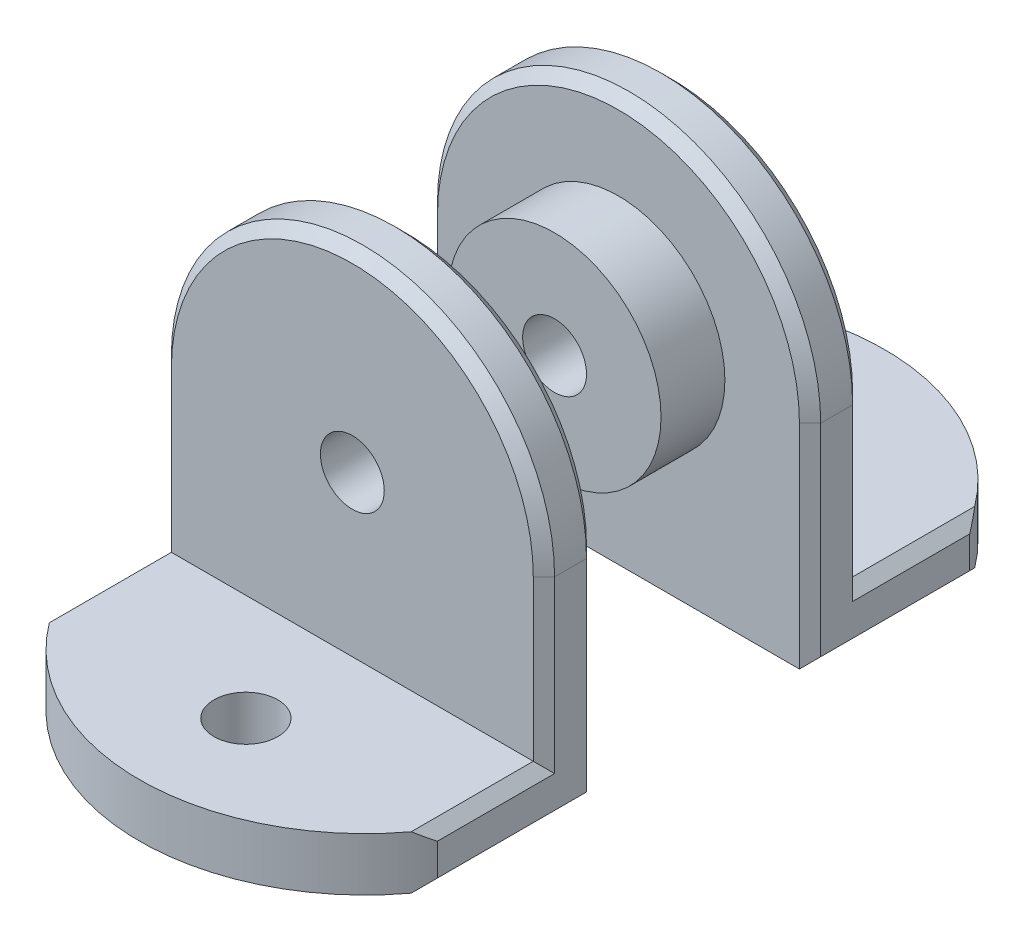
SolidWorks part; units mm, degrees
ref_plane "Front Plane" through (0, 0, 0) normal (0, 0, 1) x (1, 0, 0)
ref_plane "Top Plane" through (0, 0, 0) normal (0, 1, 0) x (1, 0, 0)
ref_plane "Right Plane" through (0, 0, 0) normal (1, 0, 0) x (0, 0, -1)
sketch "Sketch1" plane through (0, 0, 0) normal (0, 0, 1) x (1, 0, 0)
  line L0 (-18, -20) -> (18, -20)
  line L1 (18, -20) -> (18, 0)
  line L2 (-18, -20) -> (-18, 0)
  line L3 (0, 0) -> (0, -20) construction
  circle A0 centre (0, 0) radius 3
  arc A1 (18, 0) -> (-18, 0) centre (0, 0) ccw
  dimension "D2" = 36
  dimension "D4" = 6
  dimension "D1" = 36
  dimension "D3" = 20
extrude "Boss-Extrude1" add sketch "Sketch1" along normal blind 5
sketch "Sketch3" plane through (0, -20, 0) normal (0, -1, 0) x (1, 0, 0)
  line L0 (0, 0) -> (0, 15) construction
  line L1 (-18, 0) -> (18, 0)
  line L2 (-18, 0) -> (-18, 15)
  line L3 (-18, 15) -> (18, 15)
  line L4 (18, 0) -> (18, 15)
  line L5 (-18, 5) -> (18, 5) construction
  arc A0 (-18, 15) -> (18, 15) centre (0, 3.8) cw
  circle A1 centre (0, 15) radius 3
  point P13 (0, 25)
  line M8 (18, 5) -> (-18, 5)
  dimension "D1" = 6
  dimension "D2" = 10
  dimension "D3" = 10
  dimension "D4" = 15
extrude "Boss-Extrude3" add sketch "Sketch3" against normal blind 5 contours L0 L4 L3 A1 M8 | L0 A1 L3 L2 M8 | A1 L3 A0
mirror "Mirror2" about plane through (0, 0, 0) normal (0, 0, 1) of bodies 103
move or copy body "Body-Move/Copy2" bodies to move or copy 103 copy no translate (0, 0, 10)
move or copy body "Body-Move/Copy3" bodies to move or copy 105 copy no translate (0, 0, -10)
sketch "Sketch4" plane through (0, 0, -10) normal (0, 0, 1) x (1, 0, 0)
  circle A0 centre (0, 0) radius 10
  circle A1 centre (0, 0) radius 3 construction
  circle A2 centre (0, 0) radius 3
  dimension "D1" = 20
extrude "Boss-Extrude4" add sketch "Sketch4" along normal blind 6
chamfer "Chamfer1" distance 1 angle 45 10 edges at (-18, -10, 10) (0, 18, 10) (18, -10, 10) (-18, -7.5, 15) (0, 18, 15) (18, -7.5, 15) (-18, -15, 20) (-18, -20, 17.5) (18, -20, 17.5) (18, -15, 20)
chamfer "Chamfer2" distance 1 angle 45 10 edges at (-18, -20, -17.5) (-18, -15, -20) (-18, -7.5, -15) (0, 18, -15) (18, -15, -20) (18, -7.5, -15) (-18, -10, -10) (0, 18, -10) (18, -20, -17.5) (18, -10, -10)
